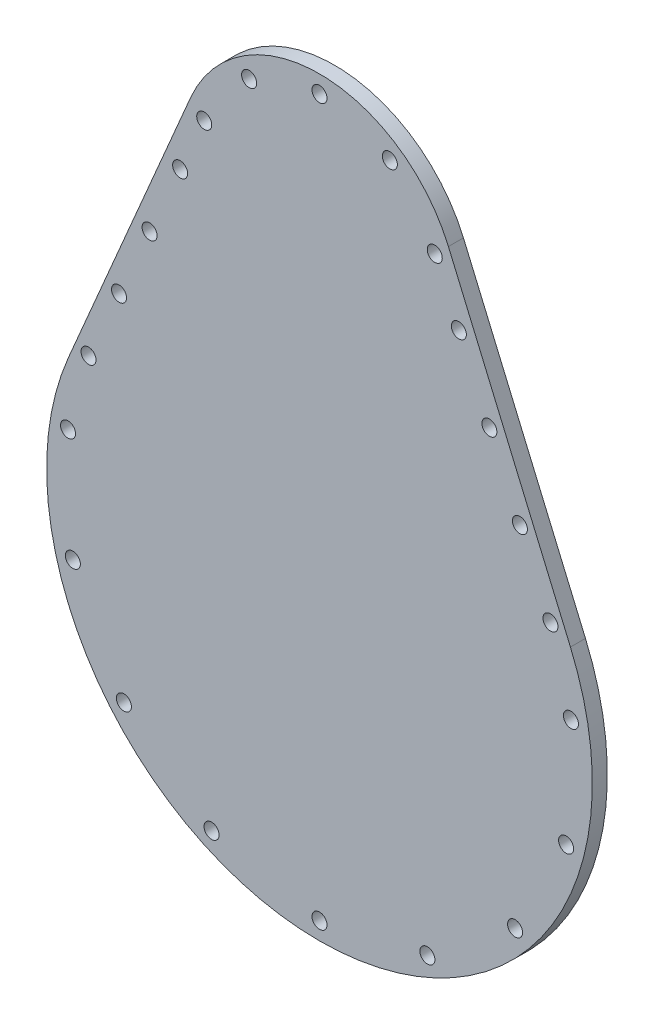
SolidWorks part; units mm, degrees
material "ABS PC"
ref_plane "Front Plane" through (0, 0, 0) normal (0, 0, 1) x (1, 0, 0)
ref_plane "Top Plane" through (0, 0, 0) normal (0, 1, 0) x (1, 0, 0)
ref_plane "Right Plane" through (0, 0, 0) normal (1, 0, 0) x (0, 0, -1)
sketch "Sketch1" plane through (0, 0, 0) normal (0, 0, 1) x (1, 0, 0)
  line L0 (0, 47) -> (0, 71.5) construction
  line L1 (-25.7519, 57.9926) -> (-50.1243, 0.8963)
  line L2 (50.1243, 0.8963) -> (25.7519, 57.9926)
  line L3 (50.2163, 0.9356) -> (25.8439, 58.0319)
  line L4 (-25.8439, 58.0319) -> (-50.2163, 0.9356)
  circle A0 centre (0, -71.5) radius 1.5
  circle A1 centre (0, 71.5) radius 1.5
  circle A2 centre (14.0526, 67.0692) radius 1.5
  circle A3 centre (23.0225, 55.3795) radius 1.5
  circle A4 centre (21.5535, -66.7217) radius 1.5
  circle A5 centre (39.0683, -53.2822) radius 1.5
  circle A6 centre (49.2622, -33.6998) radius 1.5
  circle A7 centre (50.2252, -11.6439) radius 1.5
  circle A8 centre (27.8353, 44.5559) radius 1.5
  circle A9 centre (33.9352, 30.7573) radius 1.5
  circle A10 centre (40.035, 16.9587) radius 1.5
  circle A11 centre (46.1349, 3.16) radius 1.5
  circle A12 centre (-46.1349, 3.16) radius 1.5
  circle A13 centre (-40.035, 16.9587) radius 1.5
  circle A14 centre (-33.9352, 30.7573) radius 1.5
  circle A15 centre (-27.8353, 44.5559) radius 1.5
  circle A16 centre (-50.2252, -11.6439) radius 1.5
  circle A17 centre (-49.2622, -33.6998) radius 1.5
  circle A18 centre (-39.0683, -53.2822) radius 1.5
  circle A19 centre (-21.5535, -66.7217) radius 1.5
  circle A20 centre (-23.0225, 55.3795) radius 1.5
  circle A21 centre (-14.0526, 67.0692) radius 1.5
  arc A22 (25.7519, 57.9926) -> (-25.7519, 57.9926) centre (0, 47) ccw
  arc A23 (-50.1243, 0.8963) -> (50.1243, 0.8963) centre (0, -20.5) ccw
  arc A24 (25.8439, 58.0319) -> (-25.8439, 58.0319) centre (0, 47) ccw
  arc A25 (-50.2163, 0.9356) -> (50.2163, 0.9356) centre (0, -20.5) ccw
  point P10 (0, 47)
  point P20 (0, -20.5)
  dimension "D1" = 3
  dimension "D2" = 3
  dimension "D3" = 3
  dimension "D4" = 0.1
extrude "Boss-Extrude1" add sketch "Sketch1" along normal blind 3
